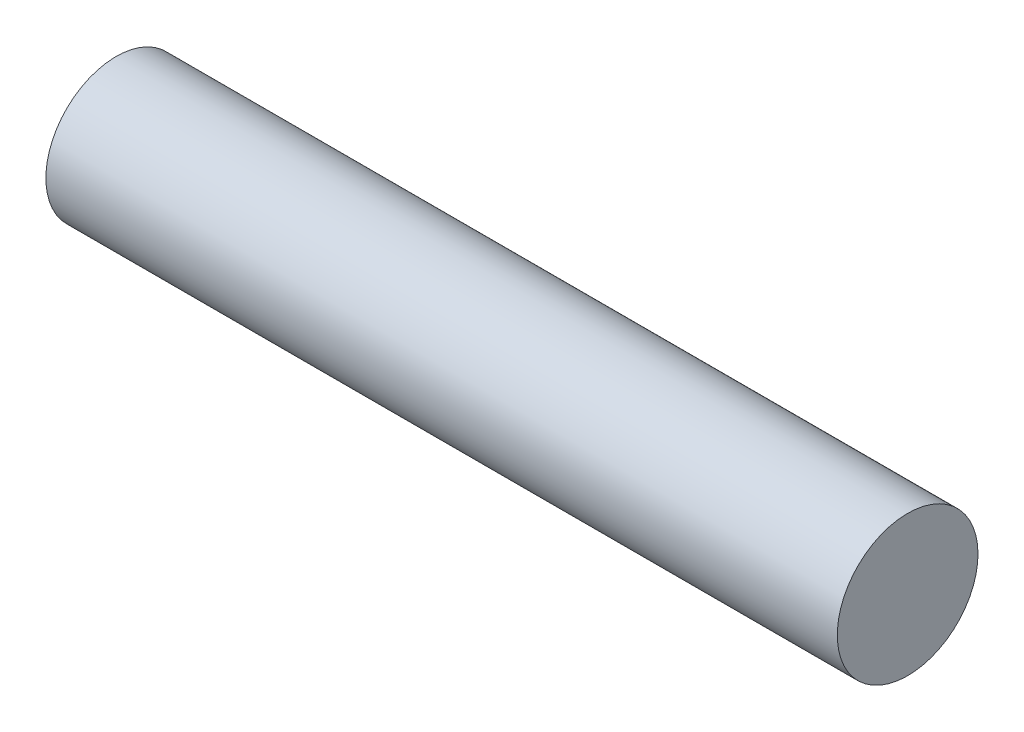
SolidWorks part; units mm, degrees
ref_plane "Alzado" through (0, 0, 0) normal (0, 0, 1) x (1, 0, 0)
ref_plane "Planta" through (0, 0, 0) normal (0, 1, 0) x (1, 0, 0)
ref_plane "Vista lateral" through (0, 0, 0) normal (1, 0, 0) x (0, 0, -1)
sketch "Croquis1" plane through (0, 0, 0) normal (1, 0, 0) x (0, 0, -1)
  circle A0 centre (0, 0) radius 4
  dimension "D1" = 8
extrude "Saliente-Extruir1" add sketch "Croquis1" along normal blind 45
